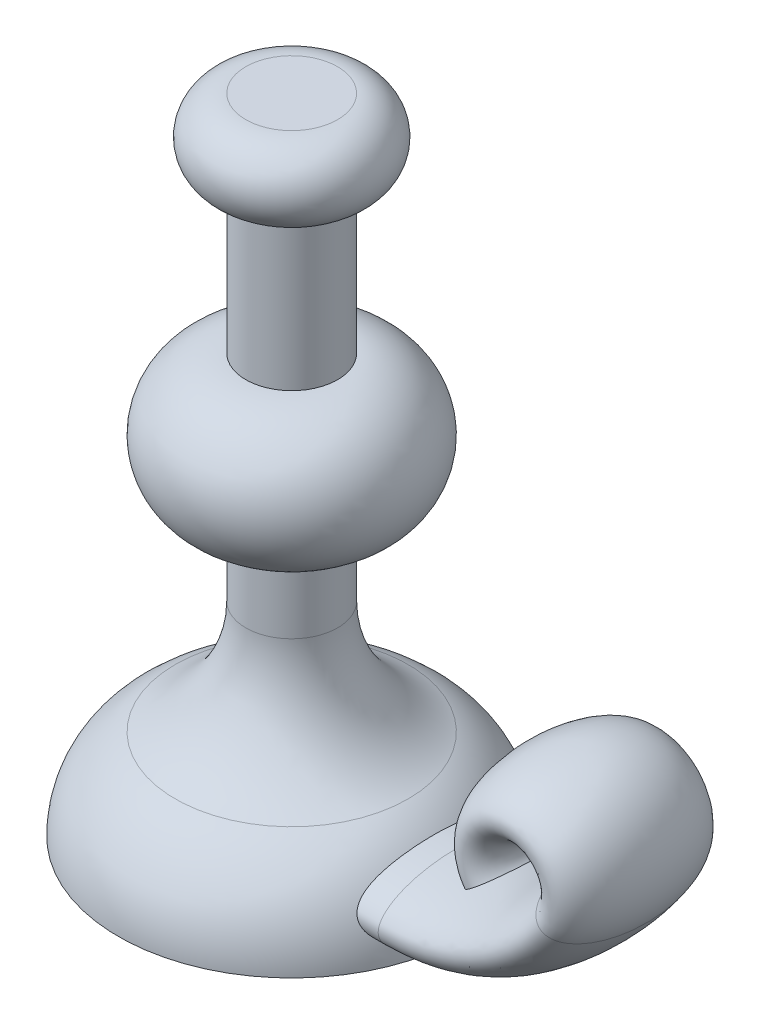
SolidWorks part; units mm, degrees
ref_plane "Front Plane" through (0, 0, 0) normal (0, 0, 1) x (1, 0, 0)
ref_plane "Top Plane" through (0, 0, 0) normal (0, 1, 0) x (1, 0, 0)
ref_plane "Right Plane" through (0, 0, 0) normal (1, 0, 0) x (0, 0, -1)
sketch "Sketch1" plane through (0, 0, 0) normal (0, 0, 1) x (1, 0, 0)
  line L0 (0, 118.0499) -> (0, -104.9471) construction
  line L1 (0, 118.0499) -> (15.9016, 118.0499)
  line L2 (15.9016, 91.9228) -> (15.9016, 40.0444)
  line L3 (15.9016, -8.8265) -> (15.9016, -34.3897)
  line L4 (60, -104.9471) -> (0, -104.9471)
  line L5 (0, 118.0499) -> (0, -104.9471)
  arc A0 (15.9016, 118.0499) -> (15.9016, 91.9228) centre (15.9016, 104.9863) cw
  arc A1 (15.9016, 40.0444) -> (15.9016, -8.8265) centre (15.9016, 15.609) cw
  arc A2 (15.9016, -34.3897) -> (40.3371, -73.4865) centre (59.3967, -34.3897) ccw
  arc A3 (40.3371, -73.4865) -> (60, -104.9471) centre (25, -104.9471) cw
  dimension "D2" = 35
  dimension "D1" = 60
revolve "Revolve1" add sketch "Sketch1" angle 360 about L0
sketch "Sketch2" plane through (0, 0, 0) normal (0, 0, 1) x (1, 0, 0)
  line L0 (0, -91.4201) -> (57.2803, -91.4201)
  arc A0 (60, -104.9471) -> (40.3371, -73.4865) centre (25, -104.9471) ccw construction
  arc A1 (57.2803, -91.4201) -> (113.5043, -62.5131) centre (57.2803, -22.289) ccw
  arc A2 (113.5043, -62.5131) -> (88.8903, -62.5131) centre (101.1973, -53.7083) ccw
ref_plane "Plane2" through (0, -91.4201, 0) normal (1, 0, 0) x (0, 0, -1)
sketch "Sketch4" plane through (0, -91.4201, 0) normal (1, 0, 0) x (0, 0, -1)
  line L0 (0, 28.907) -> (0, 0) construction
  ellipse E0 centre (0, 0) end of major axis (27.3163, 0) minor radius 11.6778
sweep "Sweep2" add profiles "Sketch4" path "Sketch2"
